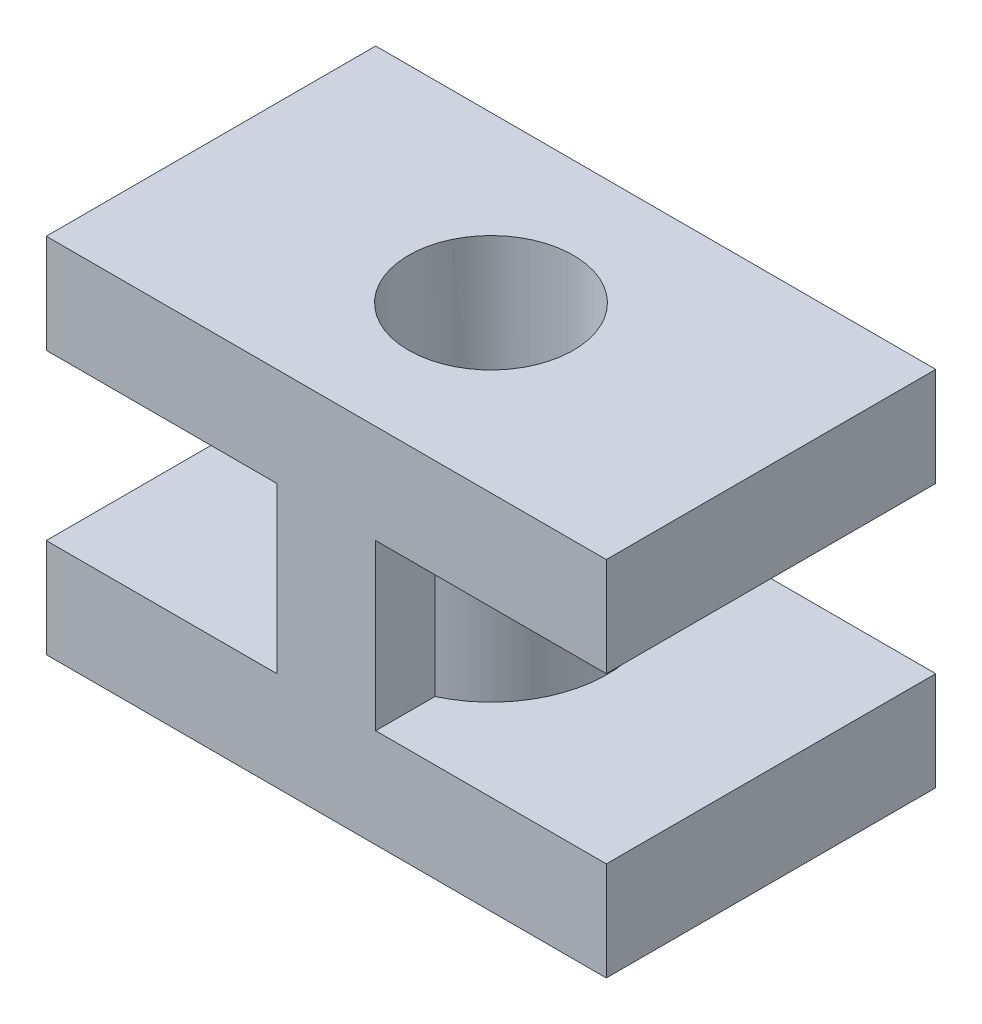
SolidWorks part; units mm, degrees
ref_plane "Front Plane" through (0, 0, 0) normal (0, 0, 1) x (1, 0, 0)
ref_plane "Top Plane" through (0, 0, 0) normal (0, 1, 0) x (1, 0, 0)
ref_plane "Right Plane" through (0, 0, 0) normal (1, 0, 0) x (0, 0, -1)
sketch "Sketch1" plane through (0, 0, 0) normal (0, 1, 0) x (1, 0, 0)
  line L1 (-4.25, -2.5) -> (4.25, -2.5)
  line L2 (-4.25, -2.5) -> (-4.25, 2.5)
  line L3 (-4.25, 2.5) -> (4.25, 2.5)
  line L4 (4.25, -2.5) -> (4.25, 2.5)
  line L5 (-4.25, -2.5) -> (4.25, 2.5) construction
  line L6 (-4.25, 2.5) -> (4.25, -2.5) construction
  point P0 (0, 0)
extrude "Boss-Extrude1" add sketch "Sketch1" along normal blind 1.5
sketch "Sketch2" plane through (0, 1.5, 0) normal (0, 1, 0) x (1, 0, 0)
  line L1 (-4.25, -2.5) -> (4.25, -2.5) construction
  line L2 (-0.75, -2.5) -> (0.75, -2.5)
  line L3 (-0.75, -2.5) -> (-0.75, -1.6008)
  line L4 (0.75, -2.5) -> (0.75, -1.6008)
  arc A1 (-0.75, -1.6008) -> (0.75, -1.6008) centre (0, 0) cw
  point P0 (0, 0)
extrude "Boss-Extrude2" add sketch "Sketch2" along normal blind 2.5
sketch "Sketch3" plane through (0, 4, 0) normal (0, 1, 0) x (1, 0, 0)
  line L1 (-4.25, -2.5) -> (4.25, -2.5)
  line L2 (-4.25, -2.5) -> (-4.25, 2.5)
  line L3 (-4.25, 2.5) -> (4.25, 2.5)
  line L4 (4.25, -2.5) -> (4.25, 2.5)
  line L5 (-4.25, -2.5) -> (4.25, 2.5) construction
  line L6 (-4.25, 2.5) -> (4.25, -2.5) construction
  point P0 (0, 0)
extrude "Boss-Extrude3" add sketch "Sketch3" along normal blind 1.5
sketch "Sketch4" plane through (0, 5.5, 0) normal (0, 1, 0) x (1, 0, 0)
  circle A0 centre (0, 0) radius 1.25
extrude "Cut-Extrude1" cut sketch "Sketch4" against normal blind 11.5
